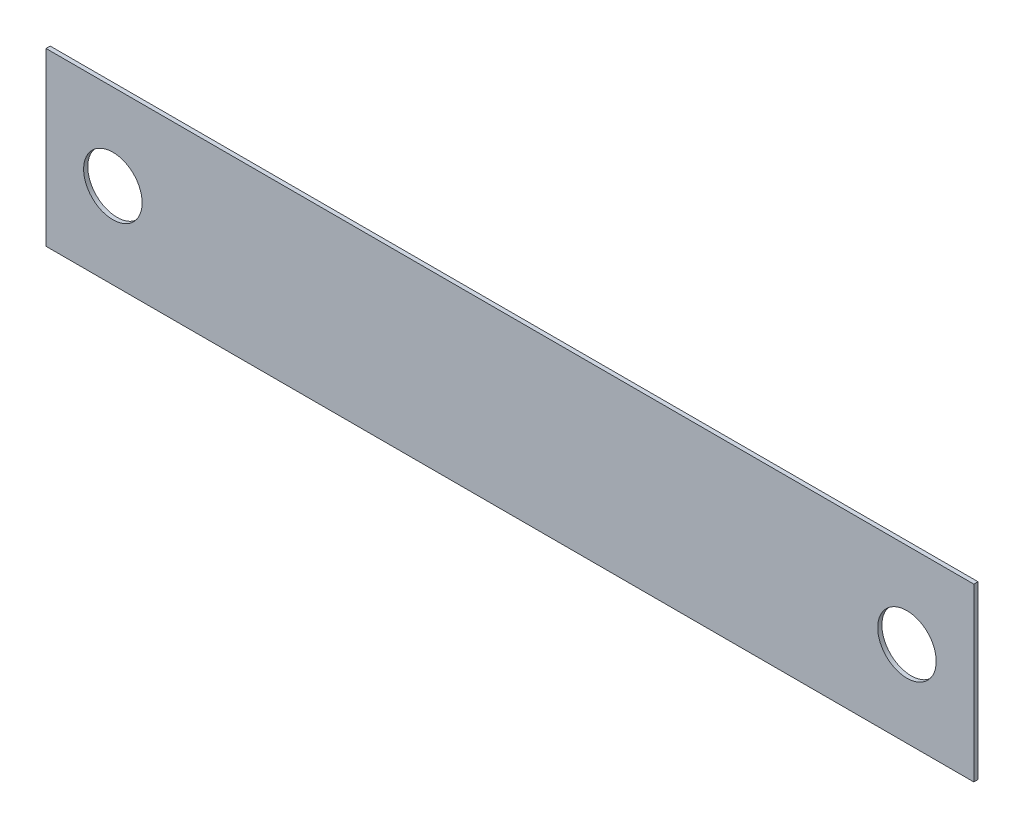
SolidWorks part; units mm, degrees
material "Chrome Stainless Steel"
ref_plane "Front Plane" through (0, 0, 0) normal (0, 0, 1) x (1, 0, 0)
ref_plane "Top Plane" through (0, 0, 0) normal (0, 1, 0) x (1, 0, 0)
ref_plane "Right Plane" through (0, 0, 0) normal (1, 0, 0) x (0, 0, -1)
sketch "Sketch1" plane through (0, 0, 0) normal (0, 0, 1) x (1, 0, 0)
  line L0 (-9.7963, 10.25) -> (119.3789, 10.25) construction
  line L1 (0, 0) -> (111, 0)
  line L2 (0, 0) -> (0, 20.5)
  line L3 (0, 20.5) -> (111, 20.5)
  line L4 (111, 0) -> (111, 20.5)
  line L5 (55.5, 25.0204) -> (55.5, -8.7281) construction
  circle A0 centre (8, 10.25) radius 3.5
  circle A1 centre (103, 10.25) radius 3.5
  dimension "D4" = 7
  dimension "D1" = 111
  dimension "D2" = 20.5
  dimension "D3" = 95
extrude "Boss-Extrude1" add sketch "Sketch1" along normal blind 0.5
